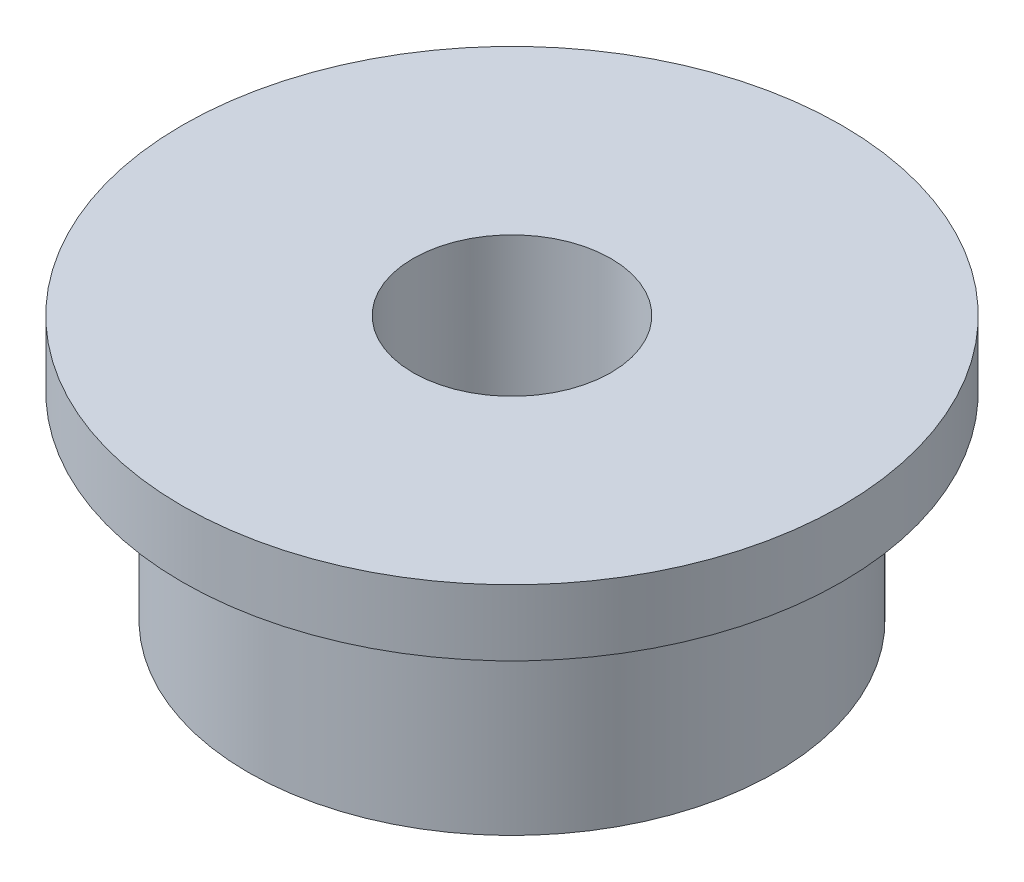
SolidWorks part; units mm, degrees
material "Plain Carbon Steel"
ref_plane "Front Plane" through (0, 0, 0) normal (0, 0, 1) x (1, 0, 0)
ref_plane "Top Plane" through (0, 0, 0) normal (0, 1, 0) x (1, 0, 0)
ref_plane "Right Plane" through (0, 0, 0) normal (1, 0, 0) x (0, 0, -1)
sketch "Sketch1" plane through (0, 0, 0) normal (0, 1, 0) x (1, 0, 0)
  circle A0 centre (0, 0) radius 5
  dimension "D1" = 10
extrude "Boss-Extrude1" add sketch "Sketch1" along normal blind 1
sketch "Sketch2" plane through (0, 0, 0) normal (0, -1, 0) x (1, 0, 0)
  circle A0 centre (0, 0) radius 4
  dimension "D1" = 8
extrude "Boss-Extrude2" add sketch "Sketch2" along normal blind 3
sketch "Sketch3" plane through (0, -3, 0) normal (0, -1, 0) x (1, 0, 0)
  circle A0 centre (0, 0) radius 1.5
  dimension "D1" = 3
extrude "Cut-Extrude1" cut sketch "Sketch3" against normal blind 13
